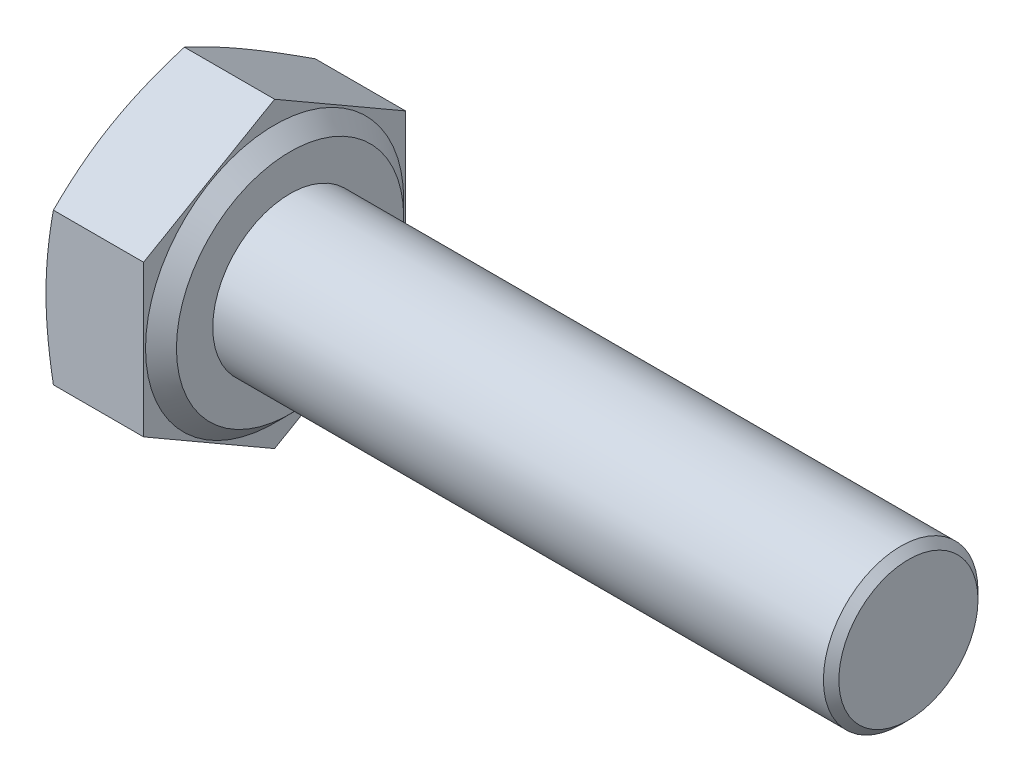
SolidWorks part; units mm, degrees
ref_plane "Front" through (0, 0, 0) normal (0, 0, 1) x (1, 0, 0)
ref_plane "Top" through (0, 0, 0) normal (0, 1, 0) x (1, 0, 0)
ref_plane "Right" through (0, 0, 0) normal (1, 0, 0) x (0, 0, -1)
sketch "Sketch2" plane through (0, 0, 0) normal (1, 0, 0) x (0, 0, -1)
  line L1 (3.39, -1.9572) -> (3.39, 1.9572)
  line L2 (3.39, 1.9572) -> (0, 3.9144)
  line L3 (0, 3.9144) -> (-3.39, 1.9572)
  line L4 (-3.39, 1.9572) -> (-3.39, -1.9572)
  line L5 (-3.39, -1.9572) -> (0, -3.9144)
  line L6 (0, -3.9144) -> (3.39, -1.9572)
  circle A0 centre (0, 0) radius 3.39 construction
  dimension "s" = 6.78
extrude "BaseHead" add sketch "Sketch2" along normal blind 2.925
sketch "Sketch3" plane through (0, 0, 0) normal (0, 0, 1) x (1, 0, 0)
  line L0 (2.925, 3.9144) -> (2.925, 2.94)
  line L2 (2.925, 2.94) -> (2.525, 3.34)
  line L3 (2.525, 3.34) -> (2.525, 3.9144)
  line L5 (2.525, 3.9144) -> (2.925, 3.9144)
  line L6 (-0.9571, 0) -> (7.6478, 0) construction
  line L7 (2.925, 3.9144) -> (0, 3.9144) construction
  dimension "D1" = 45
  dimension "c" = 0.4
  dimension "Dw" = 5.88
revolve "BearingFace" cut sketch "Sketch3" angle 360 about L6
sketch "Sketch4" plane through (0, 0, 0) normal (0, 0, 1) x (1, 0, 0)
  line L0 (-0.4935, 0) -> (3.5626, 0) construction
  line L2 (0, 3.9144) -> (0.1909, 3.9144)
  line L4 (0.1909, 3.9144) -> (0, 3.39)
  line L6 (0, 3.39) -> (0, 3.9144)
  line L7 (2.525, 3.9144) -> (0, 3.9144) construction
  dimension "D1" = 20
  dimension "D2" = 6.78
revolve "HeadChamfer" cut sketch "Sketch4" angle 360 about L0
sketch "Sketch5" plane through (2.925, 0, 0) normal (1, 0, 0) x (0, 0, -1)
  circle A0 centre (0, 0) radius 2
  dimension "d" = 4
extrude "BaseBody" add sketch "Sketch5" along normal blind 16
cosmetic thread "ThreadCosmetic1" parameters "D2"=3.242
chamfer "Chamfer1" distance 0.2 angle 45 1 edges at (18.925, 0, -2)
fillet "HeadFillet" [suppressed] radius 0.2
sketch "Sketch6" plane through (0, 0, 0) normal (0, 0, 1) x (1, 0, 0)
  line L0 (2.925, 2.379) -> (3.304, 2.379)
  line L1 (3.304, 2.379) -> (3.304, 2)
  line L2 (3.304, 2) -> (3.1145, 1.6718)
  line L3 (3.1145, 1.6718) -> (2.925, 2)
  line L4 (2.925, 2) -> (2.925, 2.379)
  line L5 (18.725, 2) -> (2.925, 2) construction
  line L6 (2.925, -2.94) -> (2.925, 2.94) construction
  dimension "D1" = 0.379
revolve "Cut-Revolve10" [suppressed] cut sketch "Sketch6" angle 360 about axis through (-0.9571, 0, 0) along (1, 0, 0)
pattern_linear "LPattern10" [suppressed] count 35
equation "\"D2@Sketch4\" = \"s@Sketch2\""
equation "\"D1@Chamfer1\" = 0.05 * \"d@Sketch5\""
equation "\"D1@Sketch6\" =  ( \"d@Sketch5\" - \"D2@ThreadCosmetic1\" )  / 2"
equation "\"pitch@LPattern10\" = \"D1@Sketch6\" * 1.2"
equation "\"D1@LPattern10\" = \"l@BaseBody\" / \"pitch@LPattern10\""
